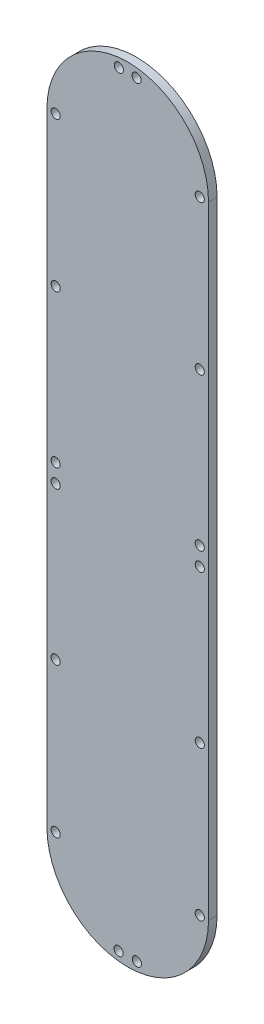
SolidWorks part; units mm, degrees
ref_plane "Front Plane" through (0, 0, 0) normal (0, 0, 1) x (1, 0, 0)
ref_plane "Top Plane" through (0, 0, 0) normal (0, 1, 0) x (1, 0, 0)
ref_plane "Right Plane" through (0, 0, 0) normal (1, 0, 0) x (0, 0, -1)
ref_plane "Plane1" through (0, 0, 0) normal (0, 0, -1) x (-1, 0, 0)
sketch "Sketch1" plane through (0, 0, 0) normal (0, 0, -1) x (-1, 0, 0)
  line L0 (5.4173, -59.5829) -> (5.4173, 171.3946)
  line L1 (-54.5827, 171.3946) -> (-54.5827, -59.5829)
  circle A0 centre (2.1673, 52.5059) radius 1.7
  circle A1 centre (-51.3327, 59.3059) radius 1.7
  circle A2 centre (-51.3327, 52.5059) radius 1.7
  circle A3 centre (-21.2827, 197.9403) radius 1.7
  circle A4 centre (2.1673, -4.0941) radius 1.7
  circle A5 centre (-51.3327, -4.0941) radius 1.7
  circle A6 centre (-51.3327, -59.5829) radius 1.7
  circle A7 centre (2.1673, 115.9059) radius 1.7
  circle A8 centre (-51.3327, 115.9059) radius 1.7
  circle A9 centre (2.1673, 171.3946) radius 1.7
  circle A10 centre (-27.9827, -86.116) radius 1.7
  circle A11 centre (2.1673, 59.3059) radius 1.7
  circle A12 centre (-51.3327, 171.3946) radius 1.7
  circle A13 centre (-21.1827, -86.116) radius 1.7
  circle A14 centre (2.1673, -59.5829) radius 1.7
  circle A15 centre (-27.8827, 197.9403) radius 1.7
  arc A16 (5.4173, 171.3946) -> (-54.5827, 171.3946) centre (-24.5827, 171.3946) ccw
  arc A17 (-54.5827, -59.5829) -> (5.4173, -59.5829) centre (-24.5827, -59.5829) ccw
extrude "Boss-Extrude1" add sketch "Sketch1" against normal blind 3.175
